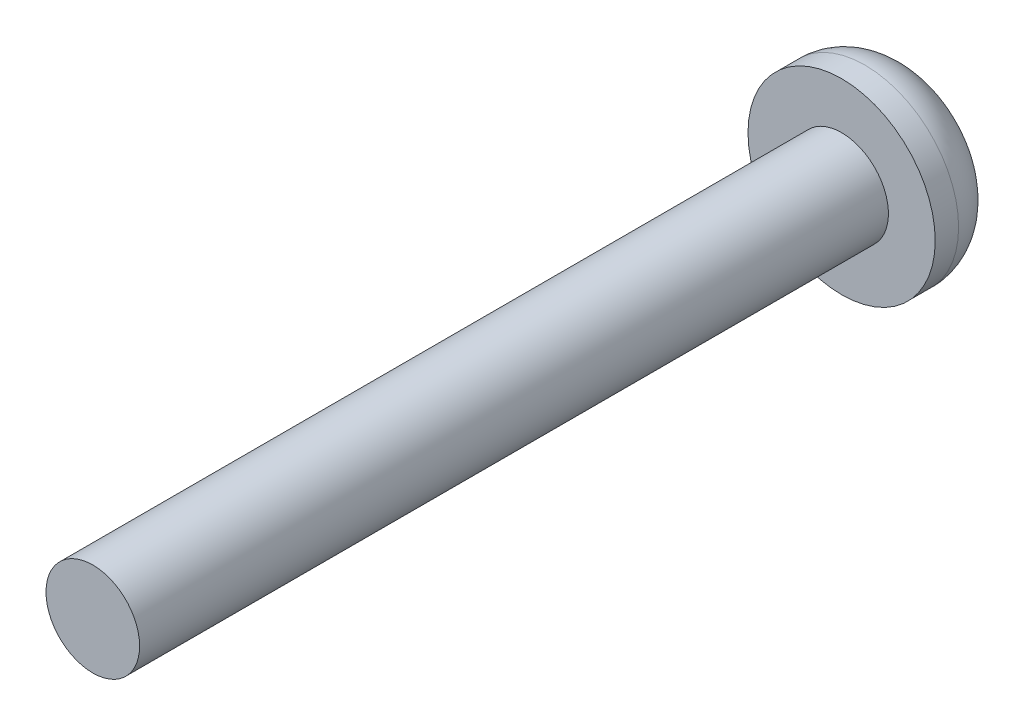
SolidWorks part; units mm, degrees
ref_plane "Front Plane" through (0, 0, 0) normal (0, 0, 1) x (1, 0, 0)
ref_plane "Top Plane" through (0, 0, 0) normal (0, 1, 0) x (1, 0, 0)
ref_plane "Right Plane" through (0, 0, 0) normal (1, 0, 0) x (0, 0, -1)
sketch "Sketch1" plane through (0, 0, 0) normal (0, 0, 1) x (1, 0, 0)
  circle A0 centre (0, 0) radius 1
extrude "Boss-Extrude1" add sketch "Sketch1" along normal blind 16
sketch "Sketch2" plane through (0, 0, 0) normal (0, 0, -1) x (-1, 0, 0)
  circle A0 centre (0, 0) radius 2
extrude "Boss-Extrude2" add sketch "Sketch2" along normal blind 1.5
fillet "Fillet1" radius 1 1 edges at (-2, 0, -1.5)
